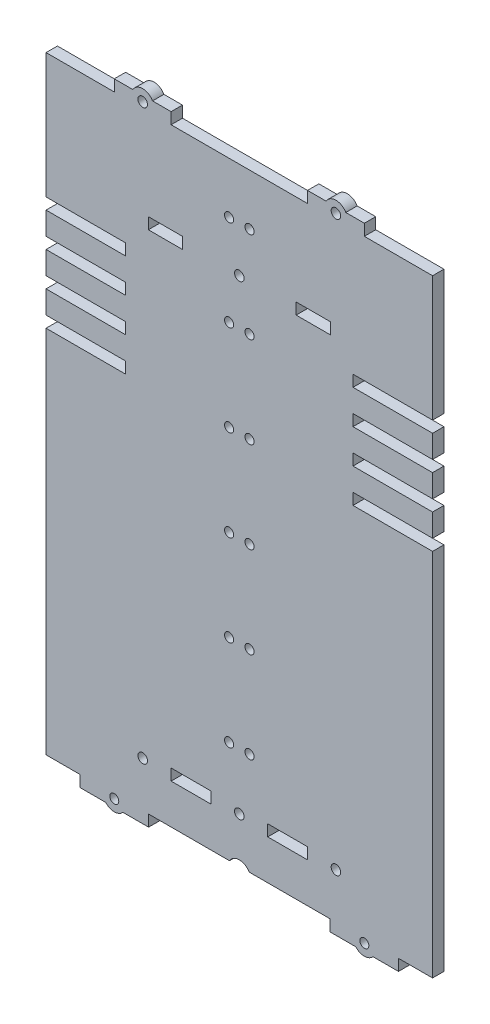
SolidWorks part; units mm, degrees
ref_plane "Front Plane" through (0, 0, 0) normal (0, 0, 1) x (1, 0, 0)
ref_plane "Top Plane" through (0, 0, 0) normal (0, 1, 0) x (1, 0, 0)
ref_plane "Right Plane" through (0, 0, 0) normal (1, 0, 0) x (0, 0, -1)
sketch "Sketch1" plane through (0, 0, 0) normal (0, 0, 1) x (1, 0, 0)
  line L1 (0, 0) -> (-170, 0)
  line L2 (0, 0) -> (0, 245)
  line L3 (0, 245) -> (-170, 245)
  line L4 (-170, 0) -> (-170, 245)
  line L5 (-125, 200) -> (-45, 200)
  line L6 (-125, 200) -> (-125, 205)
  line L7 (-125, 205) -> (-45, 205)
  line L8 (-45, 200) -> (-45, 205)
  line L9 (-110, 205) -> (-60, 205)
  line L10 (-110, 205) -> (-110, 200)
  line L11 (-110, 200) -> (-60, 200)
  line L12 (-60, 205) -> (-60, 200)
  line L94 (-170, 175) -> (-170, 170)
  line L95 (-140, 245) -> (-115, 245)
  line L96 (-140, 245) -> (-140, 250)
  line L97 (-140, 250) -> (-115, 250)
  line L98 (-115, 245) -> (-115, 250)
  line L99 (-55, 245) -> (-30, 245)
  line L100 (-55, 245) -> (-55, 250)
  line L101 (-55, 250) -> (-30, 250)
  line L102 (-30, 245) -> (-30, 250)
  line L103 (-97.5, 0) -> (-72.5, 0)
  line L104 (-97.5, 0) -> (-97.5, -5)
  line L105 (-97.5, -5) -> (-72.5, -5)
  line L106 (-72.5, 0) -> (-72.5, -5)
  line L107 (-170, 190) -> (-135, 190)
  line L108 (-170, 190) -> (-170, 185)
  line L109 (-170, 185) -> (-135, 185)
  line L110 (0, 190) -> (0, 185)
  line L111 (-135, 190) -> (-135, 185)
  line L112 (-35, 190) -> (-35, 185)
  line L113 (-170, 175) -> (-135, 175)
  line L114 (0, 175) -> (0, 170)
  line L115 (-170, 170) -> (-135, 170)
  line L116 (-135, 175) -> (-135, 170)
  line L117 (-35, 175) -> (-35, 170)
  line L118 (-170, 160) -> (-170, 155)
  line L119 (-170, 160) -> (-135, 160)
  line L120 (0, 160) -> (0, 155)
  line L121 (-170, 155) -> (-135, 155)
  line L122 (-135, 160) -> (-135, 155)
  line L123 (-35, 160) -> (-35, 155)
  line L124 (-170, 145) -> (-170, 140)
  line L125 (-170, 145) -> (-135, 145)
  line L126 (0, 145) -> (0, 140)
  line L127 (-170, 140) -> (-135, 140)
  line L128 (-135, 145) -> (-135, 140)
  line L129 (-35, 145) -> (-35, 140)
  line L130 (-170, 130) -> (-170, 125) construction
  line L131 (-170, 130) -> (-135, 130) construction
  line L132 (0, 130) -> (0, 125)
  line L133 (-170, 125) -> (-135, 125) construction
  line L134 (-135, 130) -> (-135, 125) construction
  line L135 (-35, 130) -> (-35, 125) construction
  line L136 (-170, 115) -> (-170, 110) construction
  line L137 (-170, 115) -> (-135, 115) construction
  line L138 (0, 115) -> (0, 110) construction
  line L139 (-170, 110) -> (-135, 110) construction
  line L140 (-135, 115) -> (-135, 110) construction
  line L141 (-35, 115) -> (-35, 110) construction
  line L142 (-170, 100) -> (-170, 95) construction
  line L143 (-170, 100) -> (-135, 100) construction
  line L144 (0, 100) -> (0, 95) construction
  line L145 (-170, 95) -> (-135, 95) construction
  line L146 (-135, 100) -> (-135, 95) construction
  line L147 (-35, 100) -> (-35, 95) construction
  line L148 (-170, 85) -> (-170, 80) construction
  line L149 (-170, 85) -> (-135, 85) construction
  line L150 (0, 85) -> (0, 80) construction
  line L151 (-170, 80) -> (-135, 80) construction
  line L152 (-135, 85) -> (-135, 80) construction
  line L153 (-35, 85) -> (-35, 80) construction
  line L154 (-170, 70) -> (-170, 65) construction
  line L155 (-170, 70) -> (-135, 70) construction
  line L156 (0, 70) -> (0, 65) construction
  line L157 (-170, 65) -> (-135, 65) construction
  line L158 (-135, 70) -> (-135, 65) construction
  line L159 (-35, 70) -> (-35, 65) construction
  line L160 (-170, 55) -> (-170, 50) construction
  line L161 (-170, 55) -> (-135, 55) construction
  line L162 (0, 55) -> (0, 50) construction
  line L163 (-170, 50) -> (-135, 50) construction
  line L164 (-135, 55) -> (-135, 50) construction
  line L165 (-35, 55) -> (-35, 50) construction
  line L166 (-35, 190) -> (0, 190)
  line L167 (-35, 185) -> (0, 185)
  line L168 (-35, 175) -> (0, 175)
  line L169 (-35, 170) -> (0, 170)
  line L170 (-35, 160) -> (0, 160)
  line L171 (-35, 155) -> (0, 155)
  line L172 (-35, 145) -> (0, 145)
  line L173 (-35, 140) -> (0, 140)
  line L174 (-35, 130) -> (0, 130) construction
  line L175 (-35, 125) -> (0, 125) construction
  line L176 (-35, 115) -> (0, 115) construction
  line L177 (-35, 110) -> (0, 110) construction
  line L178 (-35, 100) -> (0, 100) construction
  line L179 (-35, 95) -> (0, 95) construction
  line L180 (-35, 85) -> (0, 85) construction
  line L181 (-35, 80) -> (0, 80) construction
  line L182 (-35, 70) -> (0, 70) construction
  line L183 (-35, 65) -> (0, 65) construction
  line L184 (-35, 55) -> (0, 55) construction
  line L185 (-35, 50) -> (0, 50) construction
  point P13 (-85, 205)
  point P14 (-85, 245)
  point P107 (-85, -5)
  point P108 (-85, 0)
  dimension "D1" = 245
  dimension "D2" = 170
  dimension "D3" = 80
  dimension "D4" = 5
  dimension "D5" = 15
  dimension "D6" = 15
  dimension "D7" = 40
  dimension "D8" = 10
  dimension "D9" = 5
  dimension "D13" = 25
  dimension "D14" = 60
  dimension "D15" = 25
  dimension "D16" = 5
  dimension "D17" = 5
  dimension "D18" = 30
  dimension "D19" = 25
  dimension "D20" = 5
extrude "Boss-Extrude1" add sketch "Sketch1" along normal blind 5 contours L185 L165 L184 L2 L183 L159 L182 L181 L153 L180 L179 L147 L178 L177 L141 L176 L175 L135 L174 L173 L129 L172 L171 L123 L170 L169 L117 L168 L167 L112 L166 L3 L4 L107 L111 L109 L113 | L3 L102 L101 L100 | L3 L98 L97 L96 | L106 L1 L104 L105 | L10 L9 L12 L11
sketch "Sketch2" plane through (0, 0, 5) normal (0, 0, 1) x (1, 0, 0)
  line L1 (-123.1699, 0) -> (-131.8301, 0)
  line L2 (-85, -5) -> (-85, 5.7218) construction
  line L3 (-97.5, -5) -> (-72.5, -5) construction
  line L4 (-46.8301, 0) -> (-38.1699, 0)
  arc A0 (-123.1699, 0) -> (-131.8301, 0) centre (-127.5, -2.5) ccw
  arc A2 (-46.8301, 0) -> (-38.1699, 0) centre (-42.5, -2.5) cw
  dimension "D1" = 42.5
extrude "Cut-Extrude1" cut sketch "Sketch2" against normal blind 5
sketch "Sketch3" plane through (0, 0, 5) normal (0, 0, 1) x (1, 0, 0)
  line L0 (-97.5, 0) -> (-97.5, -5) construction
  line L1 (-97.5, -5) -> (-72.5, -5) construction
  circle A0 centre (-85, -2.5) radius 2.1
  dimension "D1" = 4.2
  dimension "D2" = 12.5
  dimension "D3" = 2.5
extrude "Cut-Extrude2" cut sketch "Sketch3" against normal blind 5
sketch "Sketch4" plane through (0, 0, 5) normal (0, 0, 1) x (1, 0, 0)
  line L0 (-97.5, -5) -> (-72.5, -5) construction
  line L1 (-89.3301, -5) -> (-80.6699, -5)
  arc A0 (-80.6699, -5) -> (-89.3301, -5) centre (-85, -2.5) cw
  dimension "D1" = 5
extrude "Boss-Extrude2" add sketch "Sketch4" against normal blind 5
sketch "Sketch5" plane through (0, 0, 5) normal (0, 0, 1) x (1, 0, 0)
  line L0 (-110, 202.5) -> (-60, 202.5) construction
  line L1 (-110, 205) -> (-110, 200) construction
  line L2 (-60, 205) -> (-60, 200) construction
  circle A0 centre (-85, 202.5) radius 2.1
  dimension "D1" = 4.2
extrude "Cut-Extrude3" cut sketch "Sketch5" against normal blind 5
sketch "Sketch6" plane through (0, 0, 5) normal (0, 0, 1) x (1, 0, 0)
  line L0 (0, 245) -> (-30, 245) construction
  line L1 (-17.1, 245) -> (-12.9, 245)
  line L2 (-17.1, 245) -> (-17.1, 240)
  line L3 (-17.1, 240) -> (-12.9, 240)
  line L4 (-12.9, 245) -> (-12.9, 240)
  line L5 (-85, 245) -> (-85, 233.1874) construction
  line L6 (-20, 240) -> (-10, 240)
  line L7 (-20, 240) -> (-20, 231.8)
  line L8 (-20, 231.8) -> (-10, 231.8)
  line L9 (-10, 240) -> (-10, 231.8)
  line L10 (-55, 245) -> (-115, 245) construction
  line L11 (-160, 240) -> (-160, 231.8)
  line L12 (-150, 231.8) -> (-160, 231.8)
  line L13 (-150, 240) -> (-150, 231.8)
  line L14 (-150, 240) -> (-160, 240)
  line L15 (-157.1, 245) -> (-157.1, 240)
  line L16 (-152.9, 240) -> (-157.1, 240)
  line L17 (-152.9, 245) -> (-152.9, 240)
  line L18 (-152.9, 245) -> (-157.1, 245)
  line L20 (-90, 231.8) -> (-80, 231.8)
  line L21 (-90, 231.8) -> (-90, 240)
  line L22 (-90, 240) -> (-80, 240)
  line L23 (-80, 231.8) -> (-80, 240)
  line L24 (-87.1, 240) -> (-82.9, 240)
  line L25 (-87.1, 240) -> (-87.1, 245)
  line L26 (-87.1, 245) -> (-82.9, 245)
  line L27 (-82.9, 240) -> (-82.9, 245)
  point P10 (-15, 231.8)
  point P11 (-15, 245)
  point P12 (-15, 245)
  point P33 (-85, 240)
  point P34 (-85, 245)
  dimension "D1" = 5
  dimension "D2" = 8.2
  dimension "D3" = 10
  dimension "D4" = 4.2
  dimension "D5" = 5
  dimension "D6" = 4.2
  dimension "D7" = 10
  dimension "D8" = 8.2
extrude "Cut-Extrude4" [suppressed] cut sketch "Sketch6" against normal blind 10
sketch "Sketch7" plane through (0, 0, 5) normal (0, 0, 1) x (1, 0, 0)
  line B0 (-55, 0) -> (-55, -5)
  line B1 (-55, -5) -> (-80.6699, -5)
  line B2 (-89.3301, -5) -> (-115, -5)
  line B3 (-115, -5) -> (-115, 0)
  line B4 (-115, 0) -> (-123.1699, 0)
  line B5 (-131.8301, 0) -> (-170, 0)
  line B6 (-170, 0) -> (-170, -22.5)
  line B7 (-170, -22.5) -> (-155, -22.5)
  line B8 (-155, -22.5) -> (-155, -27.5)
  line B9 (-155, -27.5) -> (-143.7707, -27.5)
  line B10 (-136.2293, -27.5) -> (-125, -27.5)
  line B11 (-125, -27.5) -> (-125, -22.5)
  line B12 (-125, -22.5) -> (-89.3301, -22.5)
  line B13 (-80.6699, -22.5) -> (-45, -22.5)
  line B14 (-45, -22.5) -> (-45, -27.5)
  line B15 (-45, -27.5) -> (-33.7707, -27.5)
  line B16 (-26.2293, -27.5) -> (-15, -27.5)
  line B17 (-15, -27.5) -> (-15, -22.5)
  line B18 (-15, -22.5) -> (0, -22.5)
  line B19 (0, -22.5) -> (0, 0)
  line B20 (0, 0) -> (-38.1699, 0)
  line B21 (-46.8301, 0) -> (-55, 0)
  circle B22 centre (-42.5, -2.5) radius 2.1
  circle B23 centre (-30, -24.2164) radius 1.9736
  arc B24 (-89.3301, -5) -> (-80.6699, -5) centre (-85, -2.5) ccw
  arc B25 (-123.1699, 0) -> (-131.8301, 0) centre (-127.5, -2.5) ccw
  arc B26 (-143.7707, -27.5) -> (-136.2293, -27.5) centre (-140, -24.2164) ccw
  arc B27 (-80.6699, -22.5) -> (-89.3301, -22.5) centre (-85, -25) ccw
  arc B28 (-33.7707, -27.5) -> (-26.2293, -27.5) centre (-30, -24.2164) ccw
  arc B29 (-38.1699, 0) -> (-46.8301, 0) centre (-42.5, -2.5) ccw
  circle B30 centre (-140, -24.2164) radius 1.9736
  circle B31 centre (-127.5, -2.5) radius 2.1
sketch_block_instance "Block2-1"
sketch_block "Block2"
extrude "Boss-Extrude3" add sketch "Sketch7" against normal blind 5
sketch "Sketch8" plane through (0, 0, 5) normal (0, 0, 1) x (1, 0, 0)
  line L0 (-55, 245) -> (-55, 250) construction
  line L1 (-55, 250) -> (-30, 250) construction
  line L2 (-85, 245) -> (-85, 235.328) construction
  line L3 (-55, 245) -> (-115, 245) construction
  circle A0 centre (-42.5, 247.5) radius 2.1
  circle A1 centre (-127.5, 247.5) radius 2.1
  dimension "D1" = 12.5
  dimension "D2" = 4.2
  dimension "D3" = 2.5
extrude "Cut-Extrude5" cut sketch "Sketch8" against normal blind 5
sketch "Sketch9" plane through (0, 0, 5) normal (0, 0, 1) x (1, 0, 0)
  line L0 (-55, 250) -> (-30, 250) construction
  line L1 (-46.8301, 250) -> (-38.1699, 250)
  line L2 (-85, 245) -> (-85, 235.205) construction
  line L3 (-55, 245) -> (-115, 245) construction
  line L4 (-123.1699, 250) -> (-131.8301, 250)
  arc A0 (-46.8301, 250) -> (-38.1699, 250) centre (-42.5, 247.5) cw
  arc A1 (-123.1699, 250) -> (-131.8301, 250) centre (-127.5, 247.5) ccw
  dimension "D1" = 5
extrude "Boss-Extrude4" add sketch "Sketch9" against normal blind 5
sketch "Sketch10" plane through (0, 0, 5) normal (0, 0, 1) x (1, 0, 0)
  line L0 (-85, -0.4) -> (-85, 89.5597) construction
  line L1 (-80.6699, -22.5) -> (-45, -22.5) construction
  circle A0 centre (-80.5, 22.5) radius 2
  circle A1 centre (-85, -2.5) radius 2.1 construction
  circle A2 centre (-80.5, 62.5) radius 2
  circle A3 centre (-80.5, 102.5) radius 2
  circle A4 centre (-80.5, 142.5) radius 2
  circle A5 centre (-80.5, 182.5) radius 2
  circle A6 centre (-80.5, 222.5) radius 2
  circle A8 centre (-80.5, 262.5) radius 2 [skipped]
  circle A9 centre (-89.5, 222.5) radius 2
  circle A10 centre (-89.5, 182.5) radius 2
  circle A11 centre (-89.5, 142.5) radius 2
  circle A12 centre (-89.5, 102.5) radius 2
  circle A13 centre (-89.5, 62.5) radius 2
  circle A14 centre (-89.5, 22.5) radius 2
  dimension "D1" = 4
  dimension "D2" = 4.5
  dimension "D3" = 45
  dimension "D4" = 7
extrude "Cut-Extrude6" cut sketch "Sketch10" against normal blind 10
sketch "Sketch11" plane through (-45, 0, 0) normal (-1, 0, 0) x (0, 0, 1)
  line L4 (5, -27.5) -> (5, -22.5)
  line L5 (5, -22.5) -> (0, -22.5)
  line L6 (0, -22.5) -> (0, -27.5)
  line L7 (0, -27.5) -> (5, -27.5)
  line L8 (5, -27.5) -> (5, -22.5)
  line L9 (5, -22.5) -> (0, -22.5)
  line L10 (0, -22.5) -> (0, -27.5)
  line L11 (0, -27.5) -> (5, -27.5)
  dimension "D1" = 0
extrude "Boss-Extrude5" add sketch "Sketch11" along normal blind 0.1
sketch "Sketch12" plane through (-125, 0, 0) normal (1, 0, 0) x (0, 0, -1)
  line L4 (-5, -22.5) -> (-5, -27.5)
  line L5 (-5, -27.5) -> (0, -27.5)
  line L6 (0, -27.5) -> (0, -22.5)
  line L7 (0, -22.5) -> (-5, -22.5)
  line L8 (-5, -22.5) -> (-5, -27.5)
  line L9 (-5, -27.5) -> (0, -27.5)
  line L10 (0, -27.5) -> (0, -22.5)
  line L11 (0, -22.5) -> (-5, -22.5)
  dimension "D1" = 0
extrude "Boss-Extrude6" add sketch "Sketch12" along normal blind 0.1
